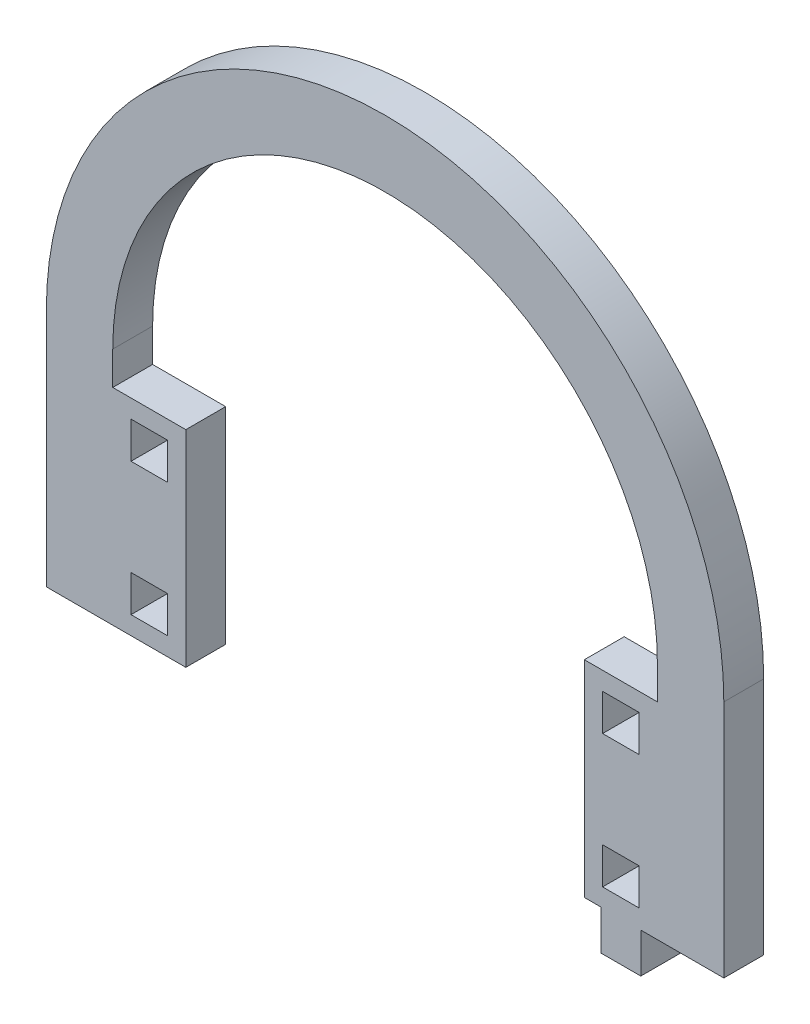
SolidWorks part; units mm, degrees
ref_plane "Front Plane" through (0, 0, 0) normal (0, 0, 1) x (1, 0, 0)
ref_plane "Top Plane" through (0, 0, 0) normal (0, 1, 0) x (1, 0, 0)
ref_plane "Right Plane" through (0, 0, 0) normal (1, 0, 0) x (0, 0, -1)
sketch "Model" plane through (0, 0, 0) normal (0, 0, 1) x (1, 0, 0)
  line L0 (3076.5328, 1463.1713) -> (3076.5328, 1427.1713)
  line L1 (3178.5328, 1463.1713) -> (3178.5328, 1427.1713)
  line L2 (3168.5328, 1463.1713) -> (3168.5328, 1458.1713)
  line L3 (3086.5328, 1463.1713) -> (3086.5328, 1458.1713)
  line L4 (3076.5328, 1427.1713) -> (3086.5328, 1427.1713)
  line L5 (3165.7828, 1435.4213) -> (3160.2828, 1435.4213)
  line L6 (3160.2828, 1435.4213) -> (3160.2828, 1429.9213)
  line L7 (3160.2828, 1429.9213) -> (3165.7828, 1429.9213)
  line L8 (3165.7828, 1429.9213) -> (3165.7828, 1435.4213)
  line L9 (3157.5328, 1427.1713) -> (3160.0328, 1427.1713)
  line L10 (3160.0328, 1427.1713) -> (3160.0328, 1421.1713)
  line L11 (3160.0328, 1421.1713) -> (3166.0328, 1421.1713)
  line L12 (3166.0328, 1421.1713) -> (3166.0328, 1427.1713)
  line L13 (3165.7828, 1455.4213) -> (3160.2828, 1455.4213)
  line L14 (3160.2828, 1455.4213) -> (3160.2828, 1449.9213)
  line L15 (3160.2828, 1449.9213) -> (3165.7828, 1449.9213)
  line L16 (3165.7828, 1449.9213) -> (3165.7828, 1455.4213)
  line L17 (3168.5328, 1458.1713) -> (3157.5328, 1458.1713)
  line L18 (3094.7828, 1435.4213) -> (3089.2828, 1435.4213)
  line L19 (3089.2828, 1435.4213) -> (3089.2828, 1429.9213)
  line L20 (3089.2828, 1429.9213) -> (3094.7828, 1429.9213)
  line L21 (3094.7828, 1429.9213) -> (3094.7828, 1435.4213)
  line L22 (3086.5328, 1427.1713) -> (3097.5328, 1427.1713)
  line L23 (3094.7828, 1455.4213) -> (3089.2828, 1455.4213)
  line L24 (3089.2828, 1455.4213) -> (3089.2828, 1449.9213)
  line L25 (3089.2828, 1449.9213) -> (3094.7828, 1449.9213)
  line L26 (3094.7828, 1449.9213) -> (3094.7828, 1455.4213)
  line L27 (3097.5328, 1458.1713) -> (3086.5328, 1458.1713)
  line L28 (3097.5328, 1458.1713) -> (3097.5328, 1427.1713)
  line L29 (3157.5328, 1458.1713) -> (3157.5328, 1427.1713)
  line L30 (3166.0328, 1427.1713) -> (3178.5328, 1427.1713)
  arc A0 (3178.5328, 1463.1713) -> (3076.5328, 1463.1713) centre (3127.5328, 1463.1713) ccw
  arc A1 (3168.5328, 1463.1713) -> (3086.5328, 1463.1713) centre (3127.5328, 1463.1713) ccw
extrude "Boss-Extrude1" add sketch "Model" along normal blind 6 contours L25 L26 L23 L24 | L20 L21 L18 L19 | L15 L16 L13 L14 | L7 L8 L5 L6 | L0 L4 L22 L28 L27 L3 A1 L2 L17 L29 L9 L10 L11 L12 L30 L1 A0
